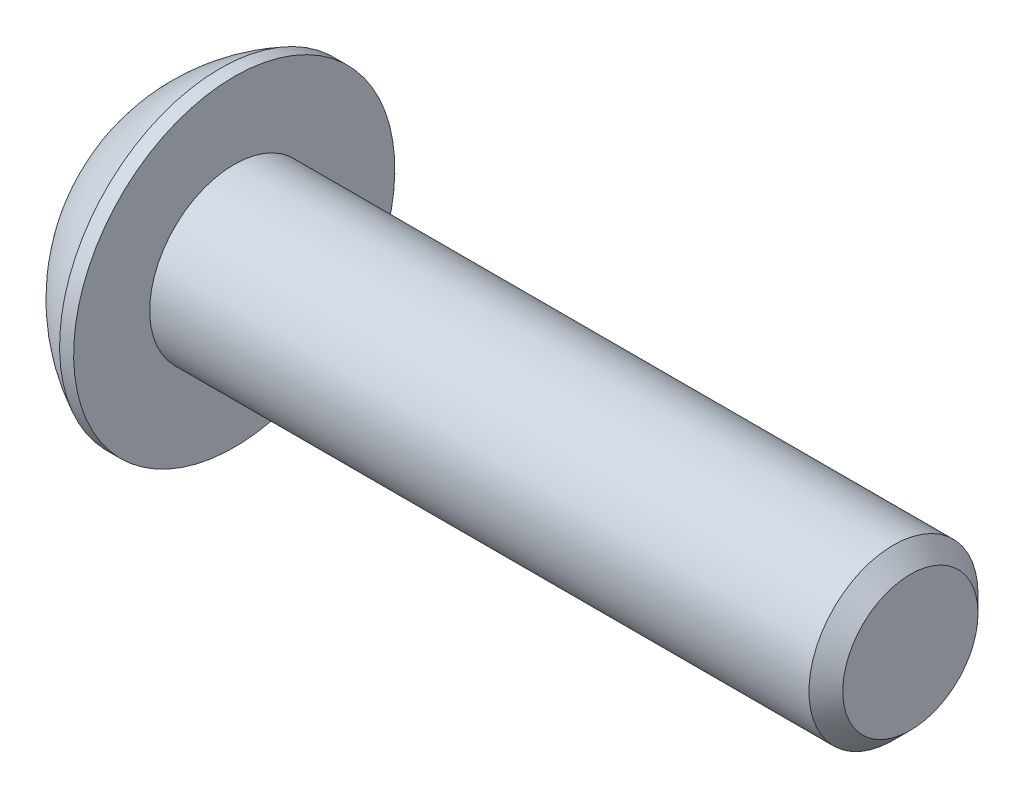
SolidWorks part; units mm, degrees
material "Plain Carbon Steel"
ref_plane "Front Plane" through (0, 0, 0) normal (0, 0, 1) x (1, 0, 0)
ref_plane "Top Plane" through (0, 0, 0) normal (0, 1, 0) x (1, 0, 0)
ref_plane "Right Plane" through (0, 0, 0) normal (1, 0, 0) x (0, 0, -1)
sketch "Sketch2" plane through (0, 0, 0) normal (1, 0, 0) x (0, 0, -1)
  circle A0 centre (0, 0) radius 1.5
  dimension "D1" = 3
extrude "Boss-Extrude1" add sketch "Sketch2" against normal blind 12
chamfer "Chamfer1" distance 0.3 angle 45 1 edges at (0, 0, -1.5)
sketch "Sketch6" plane through (0, 0, 0) normal (0, 0, 1) x (1, 0, 0)
  line L0 (-13.65, 0) -> (-13.65, 1.5)
  line L1 (-13.65, 0) -> (-12, 0)
  line L2 (-12.25, 2.85) -> (-12, 2.85)
  line L6 (-12, 2.85) -> (-12, 0)
  line L8 (-12, 0) -> (-14.6471, 0) construction
  line L10 (-12, 1.5) -> (-12, -1.5) construction
  arc A0 (-13.65, 1.5) -> (-12.25, 2.85) centre (-10.8527, 0) cw
  dimension "D3" = 0.25
  dimension "D1" = 5.7
  dimension "D2" = 1.65
  dimension "D4" = 3
revolve "Revolve1" add sketch "Sketch6" angle 360 about L8
sketch "Sketch7" plane through (-13.65, 0, 0) normal (-1, 0, 0) x (0, 0, 1)
  line L1 (0, 1.1547) -> (-1, 0.5774)
  line L2 (-1, 0.5774) -> (-1, -0.5774)
  line L3 (-1, -0.5774) -> (0, -1.1547)
  line L4 (0, -1.1547) -> (1, -0.5774)
  line L5 (1, -0.5774) -> (1, 0.5774)
  line L6 (1, 0.5774) -> (0, 1.1547)
  circle A0 centre (0, 0) radius 1 construction
  dimension "D1" = 2
extrude "Cut-Extrude1" cut sketch "Sketch7" against normal blind 1.2
sketch "Sketch8" plane through (-13.65, 0, 0) normal (-1, 0, 0) x (0, 0, 1)
  circle A0 centre (0, 0) radius 1.2047
  dimension "D1" = 0.05
extrude "Cut-Extrude2" cut sketch "Sketch8" against normal blind 1 draft 45
